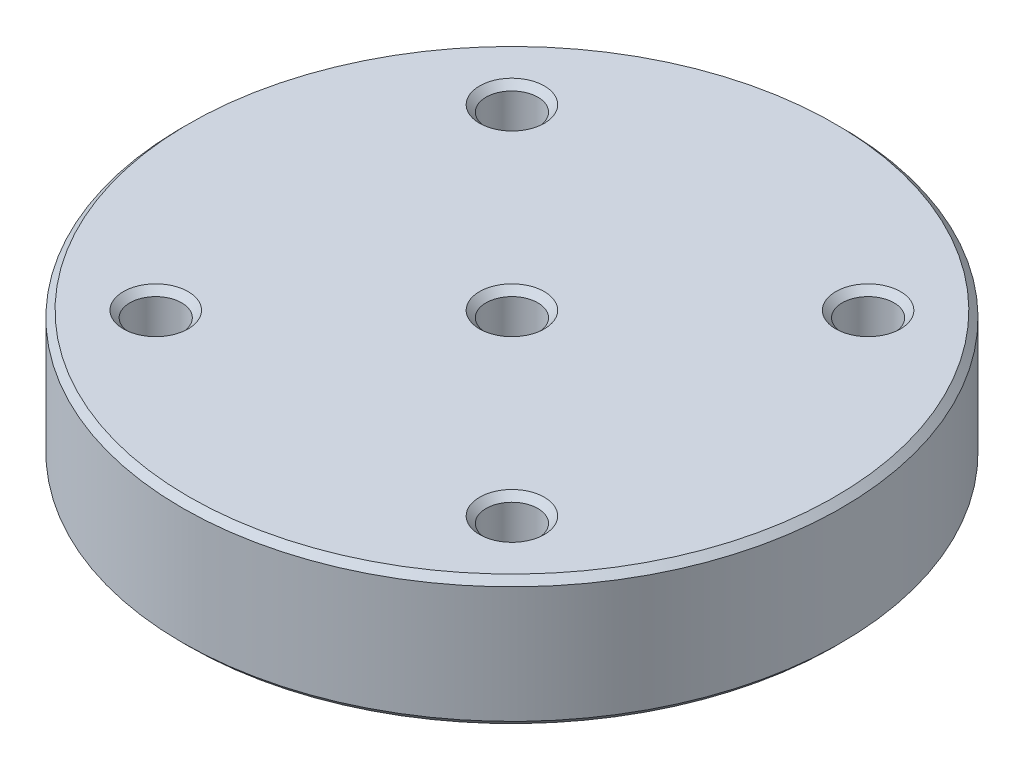
SolidWorks part; units mm, degrees
ref_plane "Front Plane" through (0, 0, 0) normal (0, 0, 1) x (1, 0, 0)
ref_plane "Top Plane" through (0, 0, 0) normal (0, 1, 0) x (1, 0, 0)
ref_plane "Right Plane" through (0, 0, 0) normal (1, 0, 0) x (0, 0, -1)
sketch "Sketch1" plane through (0, 0, 0) normal (0, 1, 0) x (1, 0, 0)
  line L1 (11, -11) -> (-11, -11) construction
  line L2 (11, -11) -> (11, 11) construction
  line L3 (11, 11) -> (-11, 11) construction
  line L4 (-11, -11) -> (-11, 11) construction
  line L5 (11, -11) -> (-11, 11) construction
  line L6 (11, 11) -> (-11, -11) construction
  circle A0 centre (0, 0) radius 1.6
  circle A1 centre (0, 0) radius 20.3563
  circle A2 centre (-11, 11) radius 1.6
  circle A3 centre (-11, 11) radius 4.8 construction
  circle A4 centre (11, 11) radius 1.6
  circle A5 centre (11, -11) radius 1.6
  circle A6 centre (-11, -11) radius 1.6
  dimension "D2" = 3.2
  dimension "D3" = 3.2
  dimension "D1" = 22
extrude "Boss-Extrude1" add sketch "Sketch1" along normal blind 8
chamfer "Chamfer1" distance 0.4 angle 45 12 edges at (-11, 0, 12.6) (11, 0, 12.6) (11, 0, -9.4) (-11, 0, -9.4) (0, 0, 1.6) (0, 0, 20.3563) (-11, 8, 12.6) (11, 8, -9.4) (0, 8, 1.6) (0, 8, 20.3563) (-11, 8, -9.4) (11, 8, 12.6)
